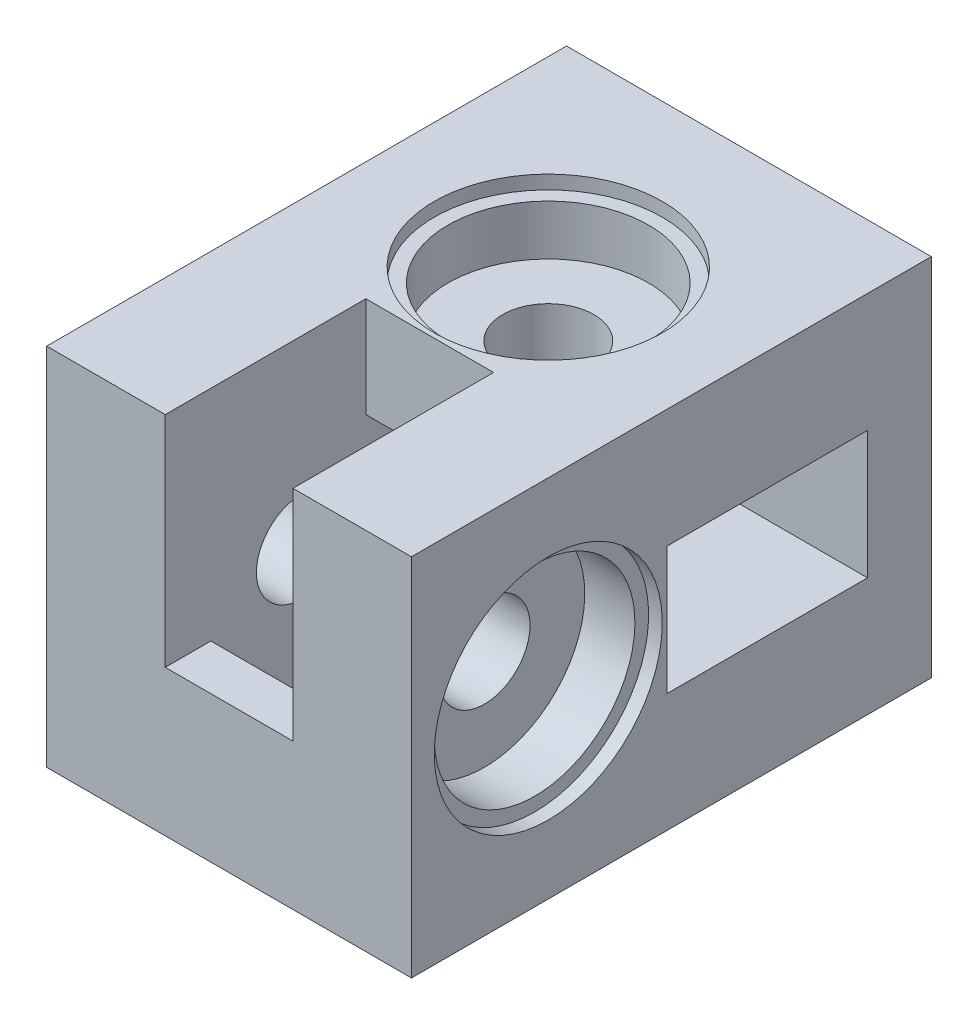
SolidWorks part; units mm, degrees
ref_plane "Plan de face" through (0, 0, 0) normal (0, 0, 1) x (1, 0, 0)
ref_plane "Plan de dessus" through (0, 0, 0) normal (0, 1, 0) x (1, 0, 0)
ref_plane "Plan de droite" through (0, 0, 0) normal (1, 0, 0) x (0, 0, -1)
sketch "Esquisse1" plane through (0, 0, 0) normal (0, 0, 1) x (1, 0, 0)
  line L1 (-40, 40) -> (0, 40)
  line L2 (-40, 40) -> (-40, 0)
  line L3 (-40, 0) -> (0, 0)
  line L4 (0, 40) -> (0, 0)
  dimension "D1" = 40
  dimension "D2" = 40
extrude "Boss.-Extru.1" add sketch "Esquisse1" along normal blind 50
sketch "Esquisse2" plane through (0, 40, 0) normal (0, 1, 0) x (1, 0, 0)
  line L0 (0, 0) -> (-40, 0) construction
  line L1 (-40, -50) -> (-40, 0) construction
  circle A0 centre (-20, -15) radius 5
  dimension "D1" = 10
  dimension "D2" = 15
  dimension "D3" = 20
extrude "Enlèv. mat.-Extru.1" cut sketch "Esquisse2" against normal through all
sketch "Esquisse3" plane through (-40, 0, 0) normal (-1, 0, 0) x (0, 0, 1)
  line L0 (50, 40) -> (50, 0) construction
  line L1 (50, 40) -> (0, 40) construction
  circle A0 centre (35, 20) radius 5
  dimension "D1" = 10
  dimension "D2" = 15
  dimension "D3" = 20
extrude "Enlèv. mat.-Extru.2" cut sketch "Esquisse3" against normal through all
sketch "Esquisse4" plane through (-40, 0, 0) normal (-1, 0, 0) x (0, 0, 1)
  line L1 (25, 27) -> (5, 27)
  line L2 (25, 27) -> (25, 13)
  line L3 (25, 13) -> (5, 13)
  line L4 (5, 27) -> (5, 13)
  line L5 (0, 40) -> (0, 0) construction
  line L6 (50, 0) -> (0, 0) construction
  line L7 (50, 40) -> (0, 40) construction
  dimension "D1" = 14
  dimension "D2" = 20
  dimension "D3" = 5
  dimension "D4" = 13
  dimension "D5" = 13
extrude "Enlèv. mat.-Extru.3" cut sketch "Esquisse4" against normal blind 29
sketch "Esquisse5" plane through (0, 0, 0) normal (0, -1, 0) x (1, 0, 0)
  line L0 (-40, 50) -> (0, 50) construction
  line L1 (-13, 25) -> (-27, 25)
  line L2 (-13, 25) -> (-13, 45)
  line L3 (-13, 45) -> (-27, 45)
  line L4 (-27, 25) -> (-27, 45)
  line L5 (-40, 50) -> (-40, 0) construction
  dimension "D1" = 20
  dimension "D2" = 5
  dimension "D3" = 14
  dimension "D4" = 13
extrude "Enlèv. mat.-Extru.4" cut sketch "Esquisse5" against normal blind 29
sketch "Esquisse6" plane through (0, 0, 0) normal (1, 0, 0) x (0, 0, -1)
  line L0 (0, 0) -> (0, 40) construction
  line L1 (0, 27) -> (-22, 27)
  line L2 (0, 27) -> (0, 13)
  line L3 (0, 13) -> (-22, 13)
  line L4 (-22, 27) -> (-22, 13)
  line L5 (-50, 0) -> (0, 0) construction
  dimension "D1" = 14
  dimension "D2" = 22
  dimension "D3" = 13
extrude "Enlèv. mat.-Extru.5" cut sketch "Esquisse6" against normal blind 24
sketch "Esquisse7" plane through (0, 40, 0) normal (0, 1, 0) x (1, 0, 0)
  line L0 (0, -50) -> (-40, -50) construction
  line L1 (-27, -50) -> (-13, -50)
  line L2 (-27, -50) -> (-27, -28)
  line L3 (-27, -28) -> (-13, -28)
  line L4 (-13, -50) -> (-13, -28)
  line L5 (-40, -50) -> (-40, 0) construction
  dimension "D1" = 14
  dimension "D2" = 22
  dimension "D3" = 13
extrude "Enlèv. mat.-Extru.6" cut sketch "Esquisse7" against normal blind 24
sketch "Esquisse8" plane through (0, 0, 0) normal (1, 0, 0) x (0, 0, -1)
  circle A0 centre (-35, 20) radius 11
  dimension "D1" = 22
extrude "Enlèv. mat.-Extru.7" cut sketch "Esquisse8" against normal blind 7
sketch "Esquisse9" plane through (0, 0, 0) normal (1, 0, 0) x (0, 0, -1)
  circle A0 centre (-35, 20) radius 12.5
  dimension "D1" = 25
extrude "Enlèv. mat.-Extru.8" cut sketch "Esquisse9" against normal blind 1.5
sketch "Esquisse10" plane through (0, 40, 0) normal (0, 1, 0) x (1, 0, 0)
  circle A0 centre (-20, -15) radius 11
  dimension "D1" = 22
extrude "Enlèv. mat.-Extru.9" cut sketch "Esquisse10" against normal blind 7
sketch "Esquisse11" plane through (0, 40, 0) normal (0, 1, 0) x (1, 0, 0)
  circle A0 centre (-20, -15) radius 12.5
  dimension "D1" = 25
extrude "Enlèv. mat.-Extru.10" cut sketch "Esquisse11" against normal blind 1.5
sketch "Esquisse12" plane through (0, 0, 0) normal (0, 0, -1) x (-1, 0, 0)
  line L1 (40, 40) -> (0, 40)
  line L2 (40, 40) -> (40, 0)
  line L3 (40, 0) -> (0, 0)
  line L4 (0, 40) -> (0, 0)
extrude "Boss.-Extru.2" add sketch "Esquisse12" along normal blind 7
sketch "Esquisse13" plane through (0, 0, -7) normal (0, 0, -1) x (-1, 0, 0)
  line L0 (40, 40) -> (0, 40) construction
  line L1 (0, 40) -> (0, 0) construction
  circle A0 centre (10, 7.5) radius 2.25
  circle A1 centre (32.5, 30) radius 2.25
  dimension "D1" = 4.5
  dimension "D2" = 4.5
  dimension "D3" = 32.5
  dimension "D4" = 32.5
  dimension "D5" = 10
  dimension "D6" = 10
extrude "Enlèv. mat.-Extru.11" cut sketch "Esquisse13" against normal blind 15
sketch "Esquisse14" plane through (-40, 0, 0) normal (-1, 0, 0) x (0, 0, 1)
  line L0 (50, 40) -> (-7, 40) construction
  line L1 (0, 33.5) -> (-3, 33.5)
  line L2 (0, 33.5) -> (0, 26.5)
  line L3 (0, 26.5) -> (-3, 26.5)
  line L4 (-3, 33.5) -> (-3, 26.5)
  line L5 (-7, 0) -> (-7, 40) construction
  dimension "D1" = 3
  dimension "D2" = 7
  dimension "D3" = 6.5
  dimension "D4" = 4
extrude "Enlèv. mat.-Extru.12" cut sketch "Esquisse14" against normal blind 12
sketch "Esquisse15" plane through (0, 0, 0) normal (0, -1, 0) x (1, 0, 0)
  line L0 (0, -7) -> (-40, -7) construction
  line L1 (-6.5, -3) -> (-13.5, -3)
  line L2 (-6.5, -3) -> (-6.5, 0)
  line L3 (-6.5, 0) -> (-13.5, 0)
  line L4 (-13.5, -3) -> (-13.5, 0)
  line L5 (0, 50) -> (0, -7) construction
  dimension "D1" = 7
  dimension "D2" = 3
  dimension "D3" = 4
  dimension "D4" = 6.5
extrude "Enlèv. mat.-Extru.13" cut sketch "Esquisse15" against normal blind 12
